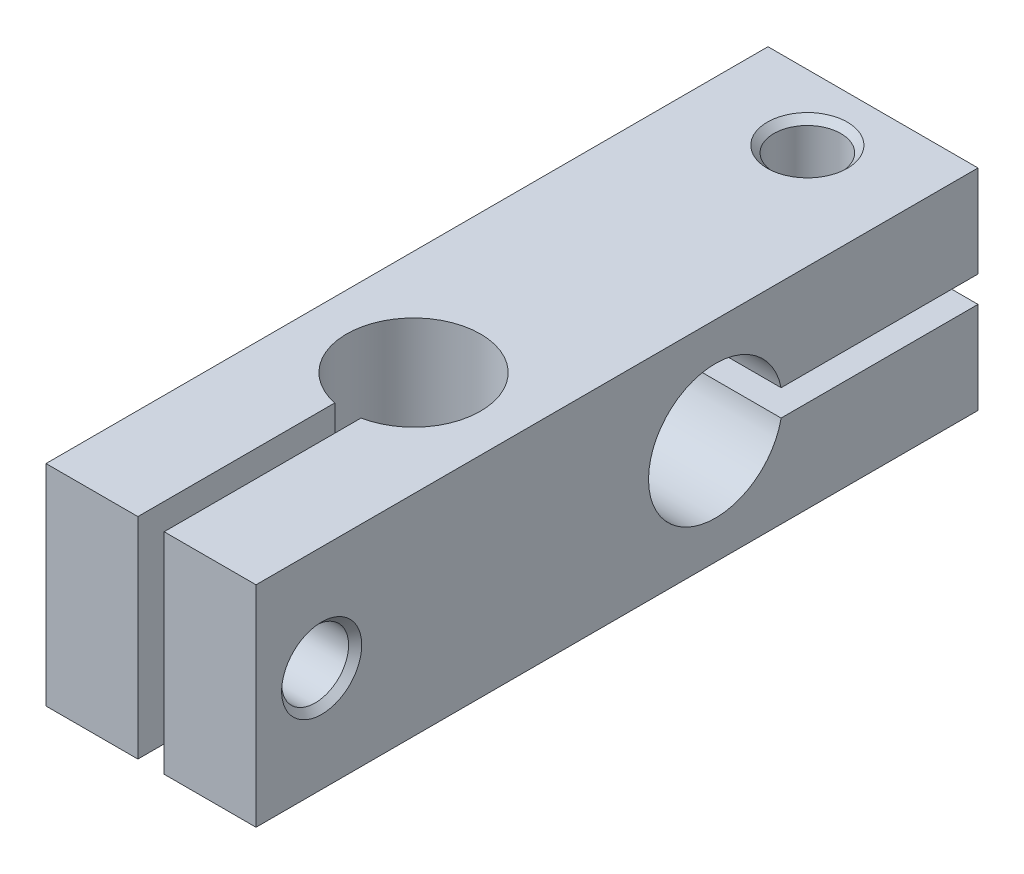
SolidWorks part; units mm, degrees
material "6063-T6"
ref_plane "Front Plane" through (0, 0, 0) normal (0, 0, 1) x (1, 0, 0)
ref_plane "Top Plane" through (0, 0, 0) normal (0, 1, 0) x (1, 0, 0)
ref_plane "Right Plane" through (0, 0, 0) normal (1, 0, 0) x (0, 0, -1)
sketch "Sketch1" plane through (0, 0, 0) normal (0, 0, 1) x (1, 0, 0)
  line L1 (8, -8) -> (-8, -8)
  line L2 (8, -8) -> (8, 8)
  line L3 (8, 8) -> (-8, 8)
  line L4 (-8, -8) -> (-8, 8)
  line L5 (8, -8) -> (-8, 8) construction
  line L6 (8, 8) -> (-8, -8) construction
  point P0 (0, 0)
  dimension "D1" = 16
  dimension "D2" = 16
extrude "Base" add sketch "Sketch1" along normal blind 55
sketch "Sketch2" plane through (0, 8, 0) normal (0, 1, 0) x (1, 0, 0)
  line L0 (-1, -55) -> (-1, -39)
  line L1 (8, -55) -> (-8, -55) construction
  line L2 (1, -55) -> (1, -39)
  line L3 (0, 0) -> (0, -9.2456) construction
  line L4 (-1, -39) -> (1, -39)
  dimension "D3" = 2
extrude "RodSlot" cut sketch "Sketch2" against normal through all
hole_wizard "Ø5.1 (5.1) free hole for screw" positions "Sketch7" profile "Sketch8" hole size "Ø5.1" standard "ANSI Metric"
sketch "Sketch7" plane through (8, 0, 0) normal (1, 0, 0) x (0, 0, -1)
  line L0 (-55, -8) -> (-55, 8) construction
  point P0 (-50, 0)
  dimension "D1" = 5
sketch "Sketch8" plane through (8, 0, 50) normal (0, 1, 0) x (0, 0, -1)
  line L0 (0, 0) -> (0, 8.5562)
  line L1 (0, 8.5562) -> (2.55, 7.5)
  line L2 (2.55, 7.5) -> (2.55, 0.5)
  line L3 (2.55, 0.5) -> (3.05, 0)
  line L5 (3.05, 0) -> (0, 0)
  line L6 (-2.55, 0.5) -> (-3.05, 0) construction
  line L10 (0, 8.5562) -> (-2.55, 7.5) construction
  line L11 (0, -6.35) -> (0, 107.95) construction
  dimension "Hole Dia." = 5.1
  dimension "Hole Depth" = 7.5
  dimension "Near C'Sink Dia." = 6.1
  dimension "Near C'Sink Angle" = 90
  dimension "Drill Angle" = 135
hole_wizard "M5x0.8 Tapped Hole for rod screw" positions "Sketch4" profile "Sketch5" tap size "M5x0.8" standard "ANSI Metric"
sketch "Sketch4" plane through (-8, 0, 0) normal (-1, 0, 0) x (0, 0, 1)
  point P0 (50, 0)
cosmetic thread "Hole Thread1" parameters "D1"=7, "D2"=5
sketch "Sketch5" plane through (-8, 0, 50) normal (0, 1, 0) x (0, 0, 1)
  line L0 (0, 0) -> (0, 8.9)
  line L1 (0, 8.9) -> (2.1, 7.6382)
  line L2 (2.1, 7.6382) -> (2.1, 0)
  line L5 (2.1, 0) -> (0, 0)
  line L10 (0, 8.9) -> (-2.1, 7.6382) construction
  line L11 (0, -6.35) -> (0, 107.95) construction
  dimension "Tap Drill Dia." = 4.2
  dimension "Tap Drill Depth" = 8.9
  dimension "Drill Angle" = 118
hole_wizard "Ø10.2 (10.2) Rod Hole" positions "Sketch11" profile "Sketch12" hole size "Ø10.2" standard "ANSI Metric" end condition through all
sketch "Sketch11" plane through (0, 8, 0) normal (0, 1, 0) x (1, 0, 0)
  line L1 (8, -55) -> (1, -55) construction
  point P0 (0, -35)
  dimension "D1" = 20
sketch "Sketch12" plane through (0, 8, 35) normal (1, 0, 0) x (0, 0, 1)
  line L0 (0, 0) -> (0, 16)
  line L1 (0, 16) -> (5.1, 16)
  line L2 (5.1, 16) -> (5.1, 0)
  line L5 (5.1, 0) -> (0, 0)
  line L11 (0, -6.35) -> (0, 107.95) construction
  dimension "Thru Hole Dia." = 10.2
  dimension "Thru Hole Depth" = 16
sketch "Sketch13" plane through (-8, 0, 0) normal (-1, 0, 0) x (0, 0, 1)
  line L0 (0, 8) -> (0, -8) construction
  line L1 (0, 1) -> (20, 1)
  line L2 (0, 1) -> (0, -1)
  line L3 (0, -1) -> (20, -1)
  line L4 (20, 1) -> (20, -1)
  point P6 (0, 0)
  point P10 (0.6636, 1)
  dimension "D1" = 2
extrude "Rod2Slot" cut sketch "Sketch13" against normal through all
hole_wizard "Ø10.2 (10.2) Rod2 Hole" positions "Sketch14" profile "Sketch15" hole size "Ø10.2" standard "ANSI Metric" end condition through all
sketch "Sketch14" plane through (-8, 0, 0) normal (-1, 0, 0) x (0, 1, 0)
  point P0 (0, -20)
  dimension "D1" = 20
sketch "Sketch15" plane through (-8, 0, 20) normal (0, 1, 0) x (0, 0, 1)
  line L0 (0, 0) -> (0, 16)
  line L1 (0, 16) -> (5.1, 16)
  line L2 (5.1, 16) -> (5.1, 0)
  line L5 (5.1, 0) -> (0, 0)
  line L11 (0, -6.35) -> (0, 107.95) construction
  dimension "Thru Hole Dia." = 10.2
  dimension "Thru Hole Depth" = 16
hole_wizard "Ø5.1 (5.1) Diameter Hole1" positions "Sketch16" profile "Sketch17" hole size "Ø5.1" standard "ANSI Metric"
sketch "Sketch16" plane through (0, 8, 0) normal (0, 1, 0) x (0, 0, -1)
  line L1 (0, -8) -> (0, 8) construction
  point P0 (-5, 0)
  dimension "D1" = 5
sketch "Sketch17" plane through (0, 8, 5) normal (1, 0, 0) x (0, 0, 1)
  line L0 (0, 0) -> (0, 8.5562)
  line L1 (0, 8.5562) -> (2.55, 7.5)
  line L2 (2.55, 7.5) -> (2.55, 0.5)
  line L3 (2.55, 0.5) -> (3.05, 0)
  line L5 (3.05, 0) -> (0, 0)
  line L6 (-2.55, 0.5) -> (-3.05, 0) construction
  line L10 (0, 8.5562) -> (-2.55, 7.5) construction
  line L11 (0, -6.35) -> (0, 107.95) construction
  dimension "Hole Dia." = 5.1
  dimension "Hole Depth" = 7.5
  dimension "Near C'Sink Dia." = 6.1
  dimension "Near C'Sink Angle" = 90
  dimension "Drill Angle" = 135
hole_wizard "M5x0.8 Tapped Hole1" positions "Sketch19" profile "Sketch20" tap size "M5x0.8" standard "ANSI Metric"
sketch "Sketch19" plane through (0, -8, 0) normal (0, -1, 0) x (-1, 0, 0)
  line L0 (8, 0) -> (-8, 0) construction
  point P0 (0, -5)
  dimension "D1" = 5
sketch "Sketch20" plane through (0, -8, 5) normal (1, 0, 0) x (0, 0, -1)
  line L0 (0, 0) -> (0, 8.9)
  line L1 (0, 8.9) -> (2.1, 7.6382)
  line L2 (2.1, 7.6382) -> (2.1, 0)
  line L5 (2.1, 0) -> (0, 0)
  line L10 (0, 8.9) -> (-2.1, 7.6382) construction
  line L11 (0, -6.35) -> (0, 107.95) construction
  dimension "Tap Drill Dia." = 4.2
  dimension "Tap Drill Depth" = 8.9
  dimension "Drill Angle" = 118
cosmetic thread "Hole Thread2" parameters "D1"=7, "D2"=5
equation "\"D2@Sketch1\"=\"D1@Sketch1\""
